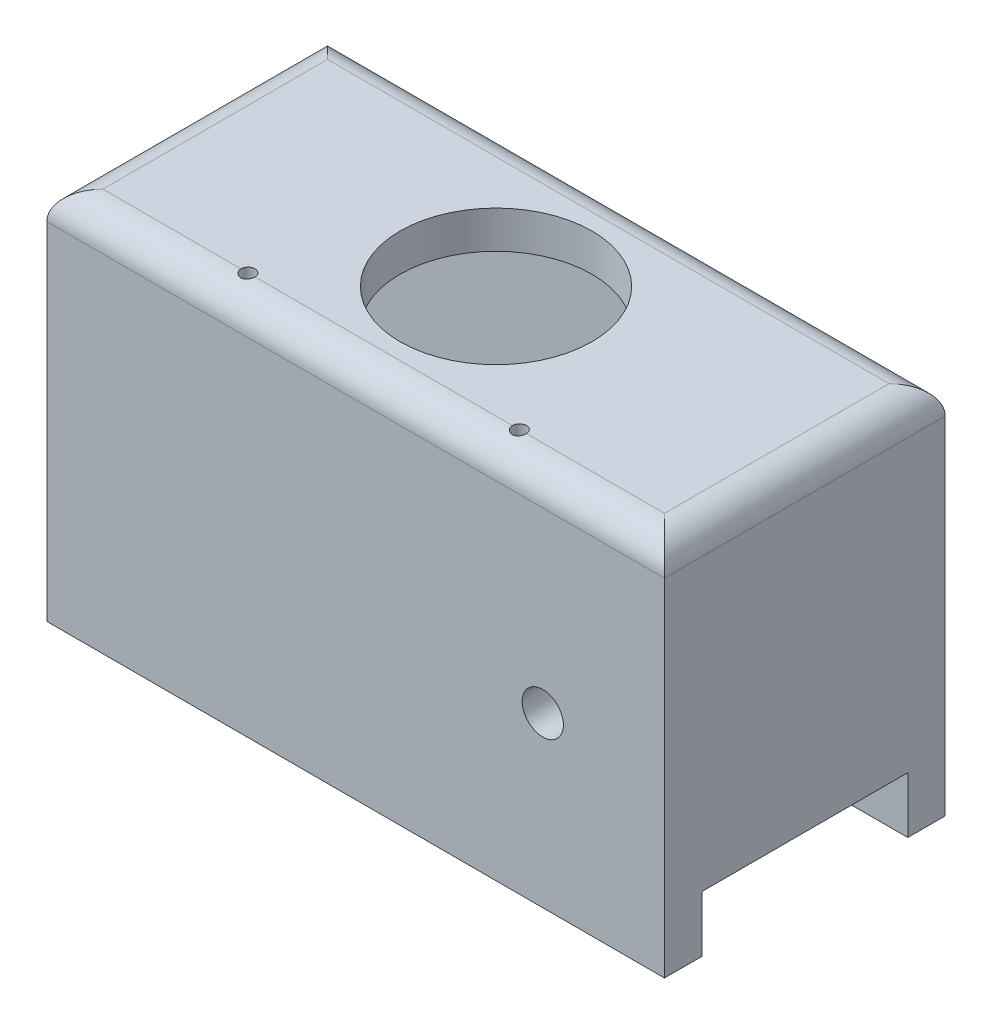
SolidWorks part; units mm, degrees
ref_plane "Front Plane" through (0, 0, 0) normal (0, 0, 1) x (1, 0, 0)
ref_plane "Top Plane" through (0, 0, 0) normal (0, 1, 0) x (1, 0, 0)
ref_plane "Right Plane" through (0, 0, 0) normal (1, 0, 0) x (0, 0, -1)
sketch "Sketch1" plane through (0, 0, 0) normal (0, 1, 0) x (1, 0, 0)
  line L1 (0, 0) -> (-66, 0)
  line L2 (0, 0) -> (0, -30)
  line L3 (0, -30) -> (-66, -30)
  line L4 (-66, 0) -> (-66, -30)
  dimension "D1" = 66
  dimension "D2" = 30
extrude "Boss-Extrude1" add sketch "Sketch1" along normal blind 4
fillet "Fillet1" radius 3 4 edges at (-33, 4, 0) (0, 4, 15) (-33, 4, 30) (-66, 4, 15)
sketch "Sketch2" plane through (0, 0, 0) normal (0, -1, 0) x (1, 0, 0)
  line L12 (-4, 4) -> (-4, 26)
  line L13 (-4, 26) -> (-62, 26)
  line L14 (-62, 26) -> (-62, 4)
  line L15 (-62, 4) -> (-4, 4)
  line L16 (-4, 4) -> (-4, 26)
  line L17 (-4, 26) -> (-62, 26)
  line L18 (-62, 26) -> (-62, 4)
  line L19 (-62, 4) -> (-4, 4)
  line L25 (0, 0) -> (0, 30)
  line L26 (0, 30) -> (-66, 30)
  line L27 (-66, 30) -> (-66, 0)
  line L28 (-66, 0) -> (0, 0)
  line L29 (0, 0) -> (0, 30)
  line L30 (0, 30) -> (-66, 30)
  line L31 (-66, 30) -> (-66, 0)
  line L32 (-66, 0) -> (0, 0)
  dimension "D2" = 0
  dimension "D1" = 4
extrude "Boss-Extrude2" add sketch "Sketch2" along normal blind 30
sketch "Sketch3" plane through (0, 4, 0) normal (0, 1, 0) x (1, 0, 0)
  line L0 (-63, -15) -> (-3, -15) construction
  line L1 (-63, -3) -> (-63, -27) construction
  line L2 (-3, -27) -> (-3, -3) construction
  line L3 (-3, -3) -> (-63, -3) construction
  line L4 (-33, -3) -> (-33, -27) construction
  line L5 (-63, -27) -> (-3, -27) construction
  circle A0 centre (-33, -15) radius 10.25
  dimension "D1" = 20.5
extrude "Cut-Extrude1" cut sketch "Sketch3" against normal through all
sketch "Sketch4" plane through (0, 4, 0) normal (0, 1, 0) x (1, 0, 0)
  line L0 (-63, -27) -> (-3, -27) construction
  line L1 (-33, -27) -> (-33, -3) construction
  line L2 (-3, -3) -> (-63, -3) construction
  circle A2 centre (-47.5, -27) radius 0.75
  circle A3 centre (-18.5, -27) radius 0.75
  dimension "D1" = 1.5
  dimension "D2" = 1.5
  dimension "D3" = 29
  dimension "D4" = 14.5
extrude "Cut-Extrude2" cut sketch "Sketch4" against normal through all
sketch "Sketch5" plane through (0, -30, 0) normal (0, -1, 0) x (1, 0, 0)
  line L0 (-66, 30) -> (-66, 0) construction
  line L1 (0, 30) -> (-66, 30)
  line L2 (0, 30) -> (0, 26)
  line L3 (0, 26) -> (-66, 26)
  line L4 (-66, 30) -> (-66, 26)
  line L5 (-4, 4) -> (0, 4) construction
  line L6 (0, 0) -> (0, 30) construction
  line L8 (-66, 0) -> (0, 0)
  line L9 (-66, 0) -> (-66, 4)
  line L10 (-66, 4) -> (0, 4)
  line L11 (0, 0) -> (0, 4)
extrude "Boss-Extrude4" add sketch "Sketch5" along normal blind 6
sketch "Sketch6" plane through (0, 0, 30) normal (0, 0, 1) x (1, 0, 0)
  line L0 (0, -36) -> (-66, -36) construction
  line L1 (0, 1) -> (0, -36) construction
  circle A0 centre (-13, -18) radius 2.2
  dimension "D1" = 4.4
  dimension "D2" = 18
  dimension "D3" = 13
extrude "Cut-Extrude3" cut sketch "Sketch6" against normal blind 6
